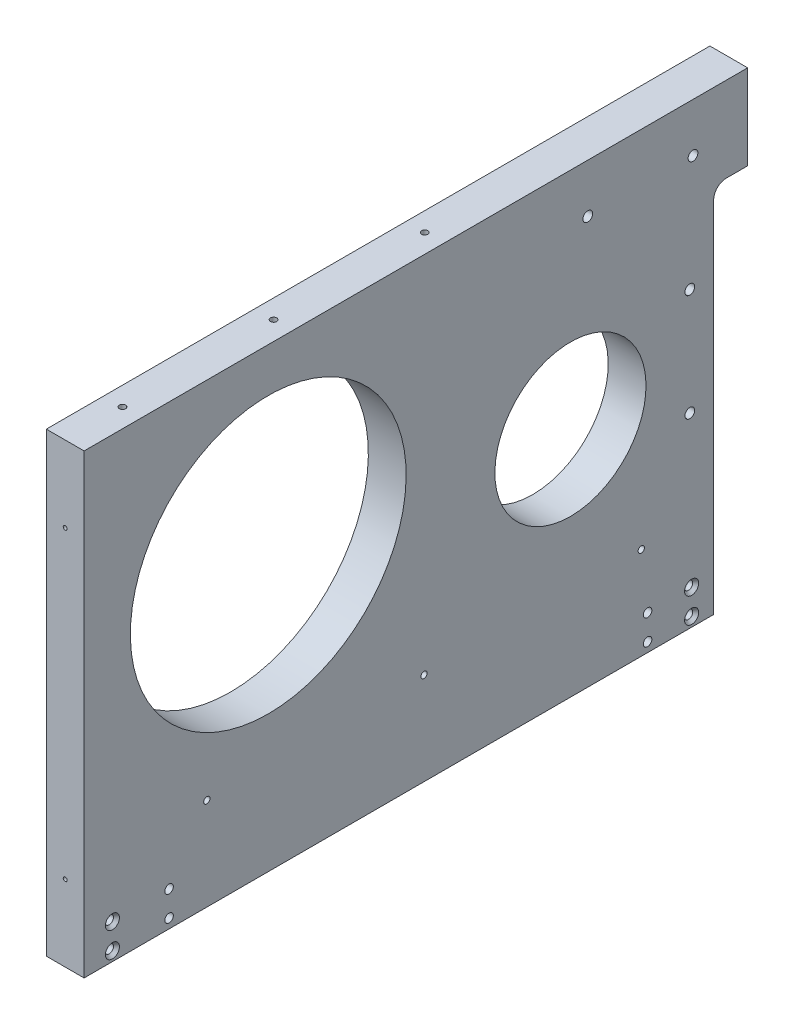
SolidWorks part; units mm, degrees
material "MDF"
ref_plane "Front Plane" through (0, 0, 0) normal (0, 0, 1) x (1, 0, 0)
ref_plane "Top Plane" through (0, 0, 0) normal (0, 1, 0) x (1, 0, 0)
ref_plane "Right Plane" through (0, 0, 0) normal (1, 0, 0) x (0, 0, -1)
sketch "Sketch1" plane through (0, 0, 0) normal (0, 0, 1) x (1, 0, 0)
  line L0 (-296.7037, -233.3625) -> (-271.672, -233.3625) construction
  line L1 (-290.722, -3.175) -> (-271.672, -3.175)
  line L2 (-290.722, -3.175) -> (-290.722, -233.3625)
  line L3 (-290.722, -233.3625) -> (-271.672, -233.3625)
  line L4 (-271.672, -3.175) -> (-271.672, -233.3625)
  dimension "D1" = 19.05
extrude "Boss-Extrude1" add sketch "Sketch1" along normal blind 342.9
sketch "Sketch2" plane through (0, 0, 0) normal (0, 0, 1) x (1, 0, 0)
  line L1 (-199.4987, -156.8808) -> (-434.4987, -156.8808) construction
  line L2 (-271.672, -3.175) -> (-290.722, -3.175) construction
  line L3 (-271.672, -156.8808) -> (-290.722, -156.8808) construction
  line L4 (-271.672, -160.0558) -> (-290.722, -160.0558)
  line L5 (-290.722, -3.175) -> (-271.672, -3.175)
  line L6 (-271.672, -160.0558) -> (-271.672, -3.175)
  line L9 (-290.722, -3.175) -> (-290.722, -160.0558)
  line L10 (-271.672, -233.3625) -> (-271.672, -3.175) construction
  line L11 (-290.722, -3.175) -> (-290.722, -233.3625) construction
  line L12 (-199.4987, -160.0558) -> (-434.4987, -160.0558) construction
  line L13 (-199.4987, -156.8808) -> (-434.4987, -156.8808) construction
  dimension "D1" = 3.175
extrude "Cut-Extrude1" cut sketch "Sketch2" along normal blind 8.255
hole_wizard "15/64 (0.23438) Diameter Hole3" positions "Sketch7" profile "Sketch8" hole size "15/64" standard "ANSI Inch"
sketch "Sketch7" plane through (-182.4037, 1936.854, -6.35) normal (0, 0, -1) x (1, 0, 0)
  point P0 (-262.8265, 2051.0885)
  point P3 (-262.8265, 2014.0687)
  point P6 (-262.8265, 1977.0488)
  point P9 (-98.7933, 2115.9598)
  point P12 (-98.7933, 2151.1665)
sketch "Sketch8" plane through (-445.2302, -114.2346, -6.35) normal (1, 0, 0) x (0, 1, 0)
  line L0 (0, 0) -> (0, 14.4885)
  line L1 (0, 14.4885) -> (2.9766, 12.7)
  line L2 (2.9766, 12.7) -> (2.9766, 0)
  line L3 (2.9766, 0) -> (0, 0)
  line L4 (0, 14.4885) -> (-2.9766, 12.7) construction
  line L5 (0, -6.35) -> (0, 107.95) construction
  dimension "Hole Dia." = 5.9533
  dimension "Hole Depth" = 12.7
  dimension "Drill Angle" = 118
hole_wizard "5/64 (0.07813) Diameter Hole1" positions "Sketch9" profile "Sketch10" hole size "5/64" standard "ANSI Inch"
sketch "Sketch9" plane through (-182.4037, 15.875, 6471.4599) normal (0, 1, 0) x (1, 0, 0)
  line L1 (-1.27, 6109.5099) -> (-1.27, 6338.7449) construction
  point P0 (-262.8265, 6157.4524)
  point P6 (-98.7933, 6157.4524)
  point P18 (-262.8265, 6233.6524)
  point P19 (-98.7933, 6233.6524)
  point P22 (-262.8265, 6309.8524)
  point P23 (-98.7933, 6309.8524)
  point P24 (-267.97, 6119.0349)
  point P34 (-115.57, 6119.0349)
  point P37 (-1.27, 6119.0349)
  point P40 (113.03, 6119.0349)
  point P44 (265.43, 6119.0349)
  point P55 (96.2533, 6309.8524)
  point P56 (260.2865, 6309.8524)
  point P59 (96.2533, 6233.6524)
  point P60 (260.2865, 6233.6524)
  point P63 (96.2533, 6157.4524)
  point P64 (260.2865, 6157.4524)
sketch "Sketch10" plane through (-445.2302, 15.875, 314.0075) normal (1, 0, 0) x (0, 0, 1)
  line L0 (0, 0) -> (0, 39.0539)
  line L1 (0, 39.0539) -> (1.5875, 38.1)
  line L2 (1.5875, 38.1) -> (1.5875, 4.0177)
  line L3 (1.5875, 4.0177) -> (5.08, 0)
  line L4 (5.08, 0) -> (0, 0)
  line L5 (-1.5875, 4.0177) -> (-5.08, 0) construction
  line L6 (0, 39.0539) -> (-1.5875, 38.1) construction
  line L7 (0, -6.35) -> (0, 107.95) construction
  dimension "Hole Dia." = 3.175
  dimension "Hole Depth" = 38.1
  dimension "Near C'Sink Dia." = 10.16
  dimension "Near C'Sink Angle" = 82
  dimension "Drill Angle" = 118
hole_wizard "5/64 (0.07813) Diameter Hole2" positions "Sketch11" profile "Sketch12" hole size "5/64" standard "ANSI Inch"
sketch "Sketch11" plane through (-182.4037, 1936.854, 361.95) normal (0, 0, 1) x (-1, 0, 0)
  line L23 (262.8265, 2088.1084) -> (262.8265, 2038.7486)
  line L24 (262.8265, 2038.7486) -> (262.8265, 1989.3888)
  line L25 (262.8265, 1989.3888) -> (262.8265, 2038.7486)
  line L26 (262.8265, 2038.7486) -> (262.8265, 1989.3888)
  line L27 (262.8265, 1989.3888) -> (262.8265, 1940.029)
  line L33 (98.7933, 2170.2165) -> (98.7933, 2131.8519)
  line L35 (98.7933, 2131.8519) -> (98.7933, 2093.4873)
  line L36 (98.7933, 2093.4873) -> (98.7933, 2055.1227)
  line L37 (98.7933, 2055.1227) -> (98.7933, 2016.7581)
  line L38 (98.7933, 2016.7581) -> (98.7933, 1978.3935)
  line L39 (98.7933, 1978.3935) -> (98.7933, 1940.029)
  line L44 (89.2683, 2123.544) -> (53.561, 2123.544)
  line L46 (53.561, 2123.544) -> (17.8537, 2123.544)
  line L47 (17.8537, 2123.544) -> (-17.8537, 2123.544)
  line L48 (-17.8537, 2123.544) -> (-53.561, 2123.544)
  line L49 (-53.561, 2123.544) -> (-89.2683, 2123.544)
  line L53 (0, 2170.2165) -> (-0.3175, 1940.029) construction
  line L55 (-99.3221, 1978.6668) -> (-99.4279, 1940.3024)
  line L56 (-99.2163, 2017.0312) -> (-99.3221, 1978.6668)
  line L57 (-99.1104, 2055.3957) -> (-99.2163, 2017.0312)
  line L58 (-99.0046, 2093.7601) -> (-99.1104, 2055.3957)
  line L59 (-98.8988, 2132.1245) -> (-99.0046, 2093.7601)
  line L60 (-98.7929, 2170.489) -> (-98.8988, 2132.1245)
  line L61 (-263.3243, 1990.1145) -> (-263.4605, 1940.7549)
  line L62 (-263.1882, 2039.4741) -> (-263.3243, 1990.1145)
  line L63 (-263.3243, 1990.1145) -> (-263.1882, 2039.4741)
  line L64 (-263.1882, 2039.4741) -> (-263.3243, 1990.1145)
  line L65 (-263.052, 2088.8338) -> (-263.1882, 2039.4741)
  point P71 (262.8265, 1964.7089)
  point P79 (262.8265, 2063.4285)
  point P95 (98.7933, 2131.8519)
  point P103 (98.7933, 1978.3935)
  point P126 (53.561, 2123.544)
  point P134 (-53.561, 2123.544)
  point P162 (-99.3221, 1978.6668)
  point P166 (-98.8988, 2132.1245)
  point P167 (-263.1201, 2064.1539)
  point P169 (-263.3924, 1965.4347)
sketch "Sketch12" plane through (80.9887, -28.5807, 361.95) normal (1, 0, 0) x (0, -1, 0)
  line L0 (0, 0) -> (0, 38.6962)
  line L1 (0, 38.6962) -> (0.9923, 38.1)
  line L2 (0.9923, 38.1) -> (0.9923, 4.7024)
  line L3 (0.9923, 4.7024) -> (5.08, 0)
  line L4 (5.08, 0) -> (0, 0)
  line L5 (-0.9923, 4.7024) -> (-5.08, 0) construction
  line L6 (0, 38.6962) -> (-0.9923, 38.1) construction
  line L7 (0, -6.35) -> (0, 107.95) construction
  dimension "Hole Dia." = 1.9845
  dimension "Hole Depth" = 38.1
  dimension "Near C'Sink Dia." = 10.16
  dimension "Near C'Sink Angle" = 82
  dimension "Drill Angle" = 118
hole_wizard "1/8 (0.125) Diameter Hole1" positions "Sketch13" profile "Sketch14" hole size "1/8" standard "ANSI Inch" end condition up to next
sketch "Sketch13" plane through (-290.722, 0, 0) normal (-1, 0, 0) x (0, 0, 1)
  line L4 (317.5, -186.69) -> (280.9875, -186.69)
  line L5 (317.5, -193.04) -> (317.5, -180.34) construction
  line L6 (280.9875, -186.69) -> (244.475, -186.69)
  line L7 (244.475, -186.69) -> (207.9625, -186.69)
  line L8 (207.9625, -186.69) -> (171.45, -186.69)
  line L9 (171.45, -186.69) -> (134.9375, -186.69)
  line L10 (134.9375, -186.69) -> (98.425, -186.69)
  line L11 (98.425, -186.69) -> (61.9125, -186.69)
  line L12 (61.9125, -186.69) -> (25.4, -186.69)
  point P10 (280.9875, -186.69)
  point P18 (171.45, -186.69)
  point P24 (61.9125, -186.69)
sketch "Sketch14" plane through (-290.722, -186.69, 61.9125) normal (0, 1, 0) x (0, 0, 1)
  line L0 (0, 0) -> (0, 19.05)
  line L1 (0, 19.05) -> (1.5875, 19.05)
  line L2 (1.5875, 19.05) -> (1.5875, 3.4925)
  line L3 (1.5875, 3.4925) -> (5.08, 0)
  line L5 (5.08, 0) -> (0, 0)
  line L6 (-1.5875, 3.4925) -> (-5.08, 0) construction
  line L11 (0, -6.35) -> (0, 107.95) construction
  dimension "Thru Hole Dia." = 3.175
  dimension "Thru Hole Depth" = 19.05
  dimension "Near C'Sink Dia." = 10.16
  dimension "Near C'Sink Angle" = 90
hole_wizard "#8 Clearance Hole1" positions "Sketch15" profile "Sketch16" hole size "#8" standard "ANSI Inch" end condition up to next
sketch "Sketch15" plane through (-271.672, 0, 0) normal (1, 0, 0) x (0, 0, -1)
  point P0 (-88.9, -27.7495)
  point P2 (-35.8275, -27.7495)
sketch "Sketch16" plane through (-271.672, -27.7495, 88.9) normal (0, 1, 0) x (0, 0, -1)
  line L0 (0, 0) -> (0, 19.05)
  line L1 (0, 19.05) -> (2.4574, 19.05)
  line L2 (2.4574, 19.05) -> (2.4574, 0)
  line L5 (2.4574, 0) -> (0, 0)
  line L11 (0, -6.35) -> (0, 107.95) construction
  dimension "Thru Hole Dia." = 4.9149
  dimension "Thru Hole Depth" = 19.05
hole_wizard "CSK for #6 Flat Head Machine Screw (100)1" positions "Sketch18" profile "Sketch19" countersink size "#6" standard "ANSI Inch" end condition up to next
sketch "Sketch18" plane through (-271.672, 0, 0) normal (1, 0, 0) x (0, 0, -1)
  point P0 (-36.5125, -215.9)
  point P3 (-36.5125, -228.6)
  point P6 (-328.6125, -215.9)
  point P9 (-328.6125, -228.6)
sketch "Sketch19" plane through (-271.672, -215.9, 36.5125) normal (0, 1, 0) x (0, 0, -1)
  line L0 (0, 0) -> (0, 19.05)
  line L1 (0, 19.05) -> (2.1526, 19.05)
  line L2 (2.1526, 19.05) -> (2.1526, 1.5998)
  line L3 (2.1526, 1.5998) -> (3.5433, 0)
  line L5 (3.5433, 0) -> (0, 0)
  line L6 (-2.1526, 1.5998) -> (-3.5433, 0) construction
  line L11 (0, -6.35) -> (0, 107.95) construction
  dimension "Thru Hole Dia." = 4.3053
  dimension "Thru Hole Depth" = 19.05
  dimension "Near C'Sink Dia." = 7.0866
  dimension "Near C'Sink Angle" = 82
hole_wizard "CSK for #6 Flat Head Machine Screw1" positions "Sketch20" profile "Sketch21" countersink size "#6" standard "ANSI Inch" end condition up to next
sketch "Sketch20" plane through (-290.722, 0, 0) normal (-1, 0, 0) x (0, 0, 1)
  point P0 (58.7375, -228.6)
  point P3 (58.7375, -215.9)
  point P6 (300.0375, -228.6)
  point P9 (300.0375, -215.9)
sketch "Sketch21" plane through (-290.722, -228.6, 58.7375) normal (0, 1, 0) x (0, 0, 1)
  line L0 (0, 0) -> (0, 19.05)
  line L1 (0, 19.05) -> (2.1526, 19.05)
  line L2 (2.1526, 19.05) -> (2.1526, 1.5998)
  line L3 (2.1526, 1.5998) -> (3.5433, 0)
  line L5 (3.5433, 0) -> (0, 0)
  line L6 (-2.1526, 1.5998) -> (-3.5433, 0) construction
  line L11 (0, -6.35) -> (0, 107.95) construction
  dimension "Thru Hole Dia." = 4.3053
  dimension "Thru Hole Depth" = 19.05
  dimension "Near C'Sink Dia." = 7.0866
  dimension "Near C'Sink Angle" = 82
sketch "Sketch22" plane through (-290.722, 0, 0) normal (-1, 0, 0) x (0, 0, 1)
  line L1 (0, -233.3625) -> (25.4, -233.3625)
  line L2 (0, -233.3625) -> (0, -45.974)
  line L3 (0, -45.974) -> (25.4, -45.974)
  line L4 (25.4, -233.3625) -> (25.4, -45.974)
  line L5 (11.33, -45.974) -> (60.325, -45.974) construction
  dimension "D1" = 25.4
extrude "Cut-Extrude3" cut sketch "Sketch22" against normal up to next
fillet "Fillet1" radius 6.35 1 edges at (-281.197, -45.974, 25.4)
hole_wizard "#8 Clearance Hole2" positions "Sketch23" profile "Sketch24" hole size "#8" standard "ANSI Inch" end condition through all
sketch "Sketch23" plane through (-271.672, 0, 0) normal (1, 0, 0) x (0, 0, -1)
  point P0 (-37.4476, -139.372)
  point P3 (-37.4476, -85.397)
sketch "Sketch24" plane through (-271.672, -139.372, 37.4476) normal (0, 1, 0) x (0, 0, -1)
  line L0 (0, 0) -> (0, 19.05)
  line L1 (0, 19.05) -> (2.4574, 19.05)
  line L2 (2.4574, 19.05) -> (2.4574, 0)
  line L5 (2.4574, 0) -> (0, 0)
  line L11 (0, -6.35) -> (0, 107.95) construction
  dimension "Thru Hole Dia." = 4.9149
  dimension "Thru Hole Depth" = 19.05
sketch "Sketch17" plane through (-290.722, 0, 0) normal (-1, 0, 0) x (0, 0, 1)
  line L0 (250.0313, -186.69) -> (250.0313, -3.175) construction
  line L2 (342.9, -3.175) -> (8.255, -3.175) construction
  line L4 (280.9875, -186.69) -> (171.45, -186.69) construction
  line L5 (97.6313, -186.69) -> (97.6313, -45.974) construction
  line L6 (60.325, -45.974) -> (117.475, -45.974) construction
  circle A0 centre (250.0313, -94.9325) radius 69.5325
  circle A1 centre (97.6313, -116.332) radius 38.1
  point P17 (250.0313, -94.9325)
  point P18 (250.0313, -164.465)
  point P19 (97.6313, -94.9325)
  point P26 (97.6313, -173.99)
  dimension "D4" = 76.2
  dimension "D1" = 22.225
  dimension "D2" = 12.7
  dimension "D3" = 152.4
extrude "Cut-Extrude2" cut sketch "Sketch17" against normal up to next
